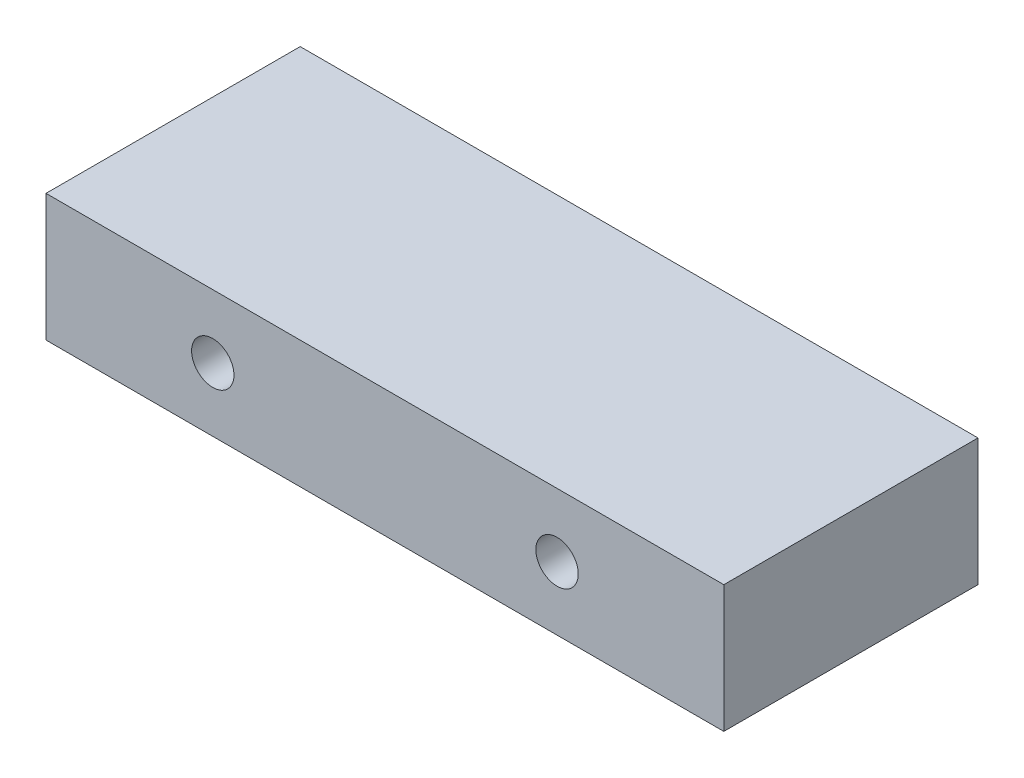
SolidWorks part; units mm, degrees
ref_plane "Front Plane" through (0, 0, 0) normal (0, 0, 1) x (1, 0, 0)
ref_plane "Top Plane" through (0, 0, 0) normal (0, 1, 0) x (1, 0, 0)
ref_plane "Right Plane" through (0, 0, 0) normal (1, 0, 0) x (0, 0, -1)
ref_plane "Plane4"
sketch "Sketch1" plane through (0, 0, 0) normal (0, 0, 1) x (1, 0, 0)
  line L0 (101.6, 19.05) -> (0, 19.05)
  line L1 (0, 19.05) -> (0, 0)
  line L2 (0, 0) -> (101.6, 0)
  line L3 (101.6, 0) -> (101.6, 19.05)
  circle A0 centre (24.9971, 9.525) radius 3.175
  circle A1 centre (76.6039, 9.525) radius 3.175
  dimension "D3" = 6.35
  dimension "D4" = 6.35
  dimension "D1" = 101.6
  dimension "D2" = 19.05
extrude "Extrusion1" add sketch "Sketch1" along normal blind 38.1 contours L2 L3 L0 L1 A1 A0
